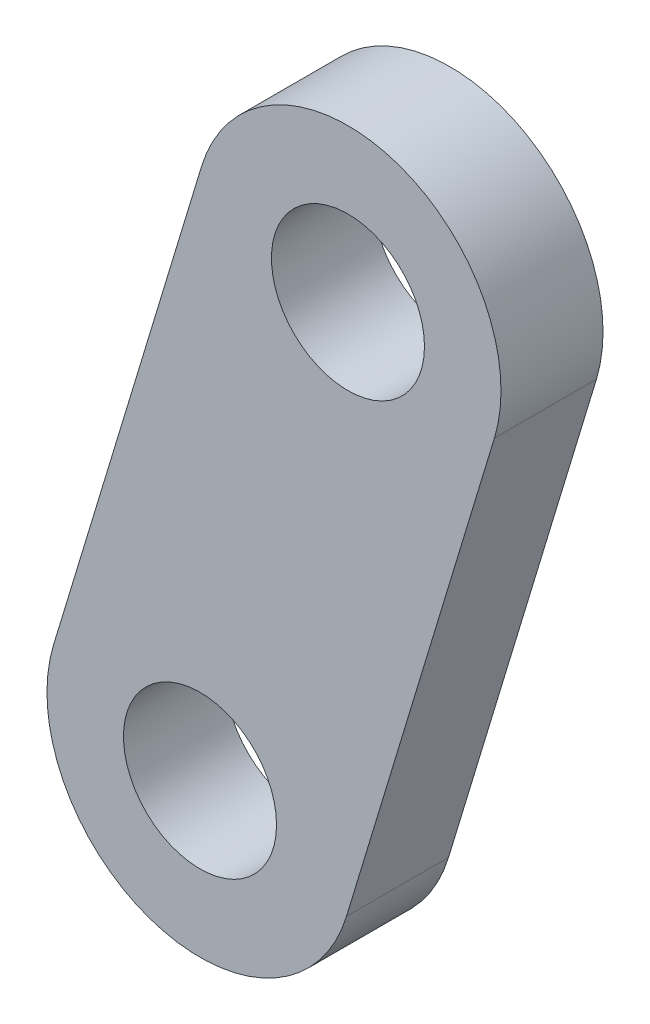
SolidWorks part; units mm, degrees
ref_plane "Front Plane" through (0, 0, 0) normal (0, 0, 1) x (1, 0, 0)
ref_plane "Top Plane" through (0, 0, 0) normal (0, 1, 0) x (1, 0, 0)
ref_plane "Right Plane" through (0, 0, 0) normal (1, 0, 0) x (0, 0, -1)
sketch "Sketch1" plane through (0, 0, 0) normal (0, 0, 1) x (1, 0, 0)
  line L0 (0, 0) -> (14.5004, 47.8512) construction
  line L1 (-14.3554, 4.3501) -> (0.145, 52.2013)
  line L2 (14.3554, -4.3501) -> (28.8557, 43.5011)
  arc A0 (-14.3554, 4.3501) -> (14.3554, -4.3501) centre (0, 0) ccw
  arc A1 (28.8557, 43.5011) -> (0.145, 52.2013) centre (14.5004, 47.8512) ccw
  circle A2 centre (0, 0) radius 7.5
  circle A3 centre (14.5004, 47.8512) radius 7.5
  point P3 (7.2502, 23.9256)
  dimension "D2" = 15
  dimension "D3" = 15
  dimension "D4" = 15
  dimension "D1" = 50
extrude "Boss-Extrude2" add sketch "Sketch1" along normal blind 10
